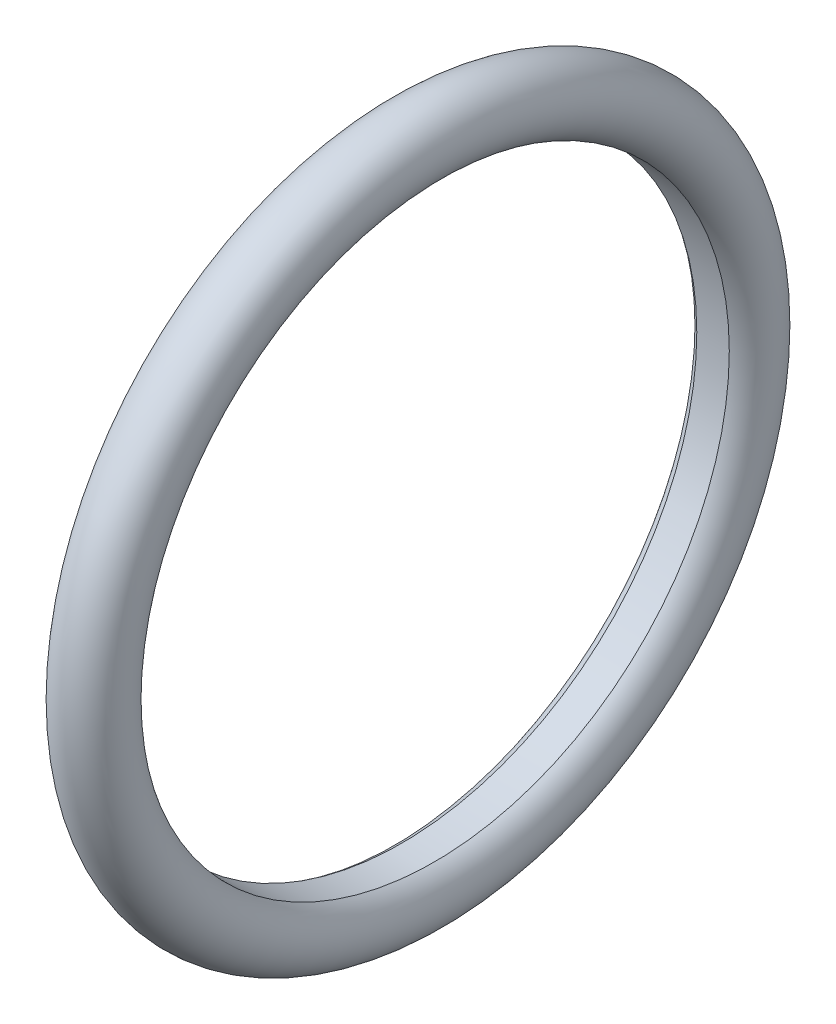
SolidWorks part; units mm, degrees
material "POLYURETHANE (11671)"
ref_plane "Front Plane" through (0, 0, 0) normal (0, 0, 1) x (1, 0, 0)
ref_plane "Top Plane" through (0, 0, 0) normal (0, 1, 0) x (1, 0, 0)
ref_plane "Right Plane" through (0, 0, 0) normal (1, 0, 0) x (0, 0, -1)
sketch "Sketch1" plane through (0, 0, 0) normal (0, 0, 1) x (1, 0, 0)
  line L0 (-1000, 0) -> (49000, 0) construction
  circle A0 centre (0, 19.325) radius 2
  dimension "D1" = 4
  dimension "D2" = 19.325
revolve "Revolve1" add sketch "Sketch1" angle 360 about L0
sketch "Sketch2" plane through (0, 0, 0) normal (1, 0, 0) x (0, 0, -1)
  circle A0 centre (0, 0) radius 17.575
  dimension "D1" = 35.15
extrude "Cut-Extrude3" cut sketch "Sketch2" against normal mid plane 2
